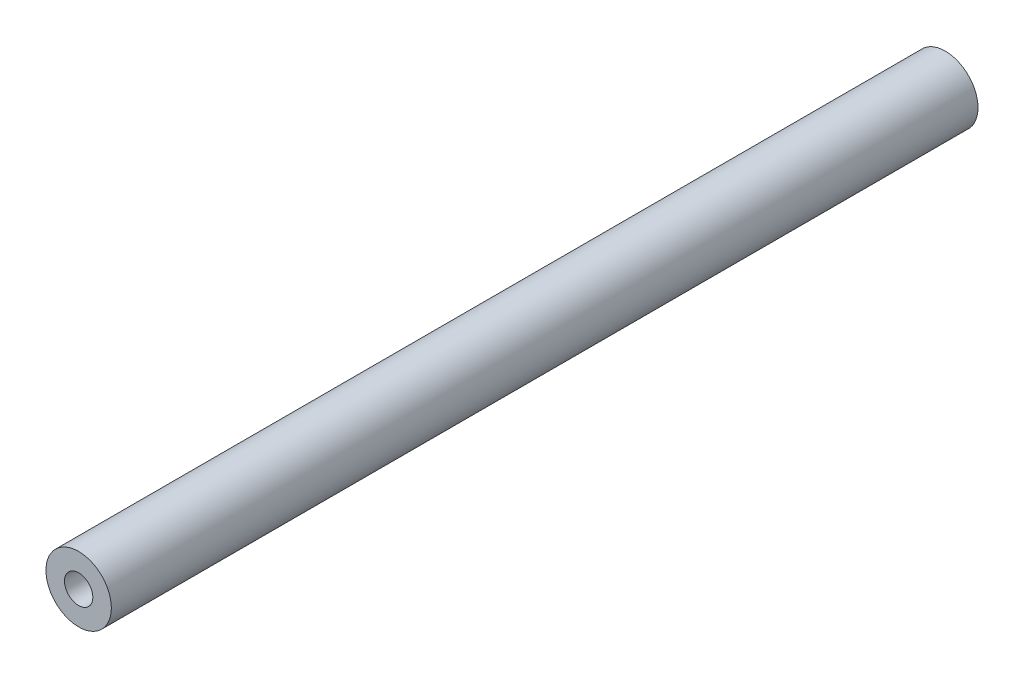
SolidWorks part; units mm, degrees
material "1023 Carbon Steel Sheet (SS)"
ref_plane "Front Plane" through (0, 0, 0) normal (0, 0, 1) x (1, 0, 0)
ref_plane "Top Plane" through (0, 0, 0) normal (0, 1, 0) x (1, 0, 0)
ref_plane "Right Plane" through (0, 0, 0) normal (1, 0, 0) x (0, 0, -1)
sketch "Sketch1" plane through (0, 0, 0) normal (0, 0, 1) x (1, 0, 0)
  circle A0 centre (0, 0) radius 6
  dimension "D1" = 12
extrude "Boss-Extrude1" add sketch "Sketch1" along normal blind 100 and the other way offset from surface (59 mm away) 2
hole_wizard "Tap Drill for M5 Helicoil1" positions "Sketch4" profile "Sketch5" hole size "M5x0.8" standard "ANSI Metric"
sketch "Sketch4" plane through (0, 0, 100) normal (0, 0, 1) x (1, 0, 0)
  point P0 (0, 0)
sketch "Sketch5" plane through (0, 0, 100) normal (1, 0, 0) x (0, -1, 0)
  line L0 (0, 0) -> (0, 31.5622)
  line L1 (0, 31.5622) -> (2.6, 30)
  line L2 (2.6, 30) -> (2.6, 0)
  line L5 (2.6, 0) -> (0, 0)
  line L10 (0, 31.5622) -> (-2.6, 30) construction
  line L11 (0, -6.35) -> (0, 107.95) construction
  dimension "Hole Dia." = 5.2
  dimension "Hole Depth" = 30
  dimension "Drill Angle" = 118
hole_wizard "Tap Drill for M5 Helicoil2" positions "Sketch6" profile "Sketch7" hole size "M5x0.8" standard "ANSI Metric"
sketch "Sketch6" plane through (0, 0, -59) normal (0, 0, -1) x (-1, 0, 0)
  point P0 (0, 0)
sketch "Sketch7" plane through (0, 0, -59) normal (1, 0, 0) x (0, 1, 0)
  line L0 (0, 0) -> (0, 31.5622)
  line L1 (0, 31.5622) -> (2.6, 30)
  line L2 (2.6, 30) -> (2.6, 0)
  line L5 (2.6, 0) -> (0, 0)
  line L10 (0, 31.5622) -> (-2.6, 30) construction
  line L11 (0, -6.35) -> (0, 107.95) construction
  dimension "Hole Dia." = 5.2
  dimension "Hole Depth" = 30
  dimension "Drill Angle" = 118
equation "\"tubeOutDiameter\" = 35mm"
equation "\"wheelShaftDiameter\"= 12mm"
equation "\"wheelThickness\"= 135mm"
equation "\"BearingDiameter\"= 20mm"
equation "\"BearingThickness\"= 10mm"
